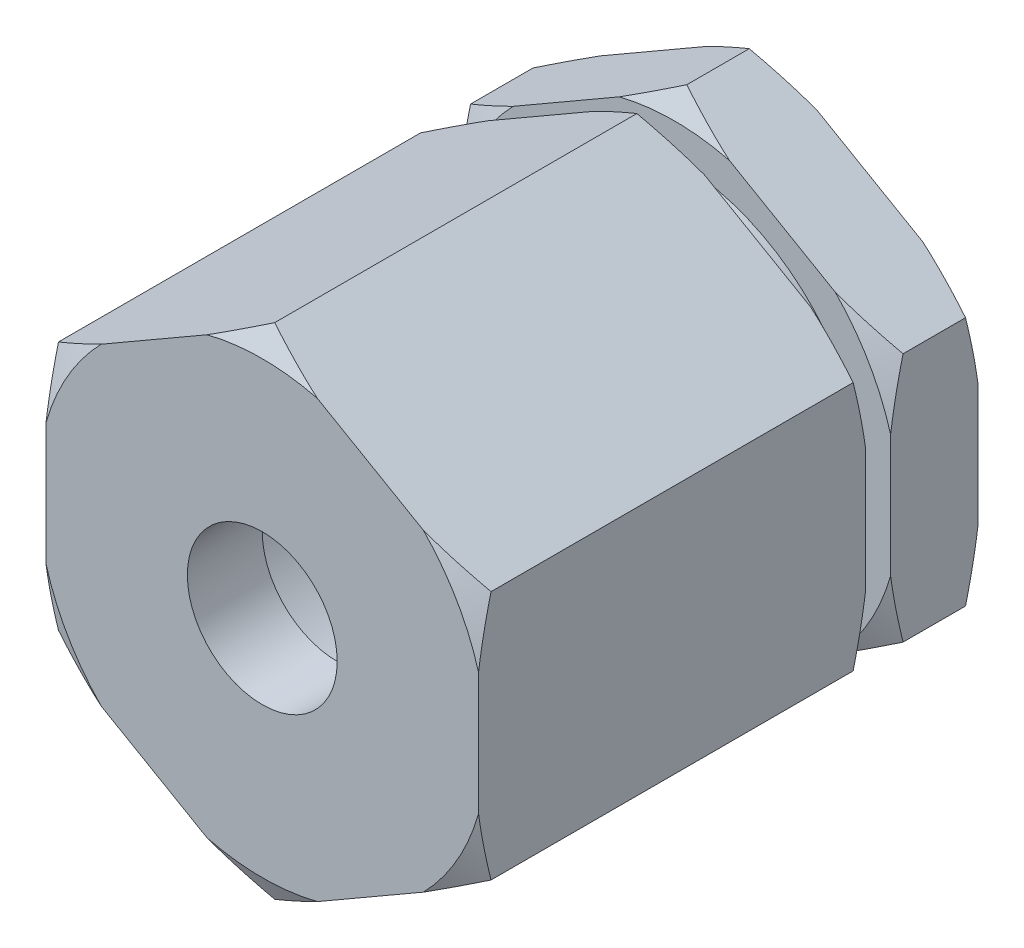
SolidWorks part; units mm, degrees
ref_plane "Plano frontal" through (0, 0, 0) normal (0, 0, 1) x (1, 0, 0)
ref_plane "Plano superior" through (0, 0, 0) normal (0, 1, 0) x (1, 0, 0)
ref_plane "Plano direito" through (0, 0, 0) normal (1, 0, 0) x (0, 0, -1)
sketch "Esboço2" plane through (0, 0, 0) normal (0, 0, 1) x (1, 0, 0)
  line L0 (-8.6603, 5) -> (-8.6603, -5)
  line L5 (8.6603, -5) -> (8.6603, 5)
  line L6 (8.6603, 5) -> (0, 10)
  line L7 (0, 10) -> (-8.6603, 5)
  line L8 (-8.6603, -5) -> (0, -10)
  line L9 (0, -10) -> (8.6603, -5)
  circle A1 centre (0, 0) radius 3
extrude "Ressalto-extrusão1" add sketch "Esboço2" along normal blind 20
sketch "Esboço3" plane through (0, 0, 0) normal (0, 0, -1) x (-1, 0, 0)
  circle A0 centre (0, 0) radius 6
extrude "Corte-extrusão1" cut sketch "Esboço3" against normal blind 17
ref_axis "Eixo1" through (0, 0, 21) along (0, 0, -1)
sketch "Esboço6" plane through (0, 0, 0) normal (0, 1, 0) x (1, 0, 0)
  line L0 (-8.6603, -3.5) -> (-10.0945, -3.5)
  line L1 (-8.6603, -20) -> (-8.6603, 0) construction
  line L2 (-10.0945, -3.5) -> (-10.0945, -4.5)
  line L3 (-8.6603, -4.5) -> (-10.0945, -4.5)
  line L9 (-8.6603, -3.5) -> (-7.6603, -3.5)
  line L10 (-7.6603, -3.5) -> (-7.6603, -4.5)
  line L11 (-7.6603, -4.5) -> (-8.6603, -4.5)
revolve "Corte-Revolução3" cut sketch "Esboço6" angle 360 about axis through (0, 0, 21) along (0, 0, -1)
sketch "Esboço11" plane through (0, 0, 0) normal (1, 0, 0) x (0, 0, -1)
  line L1 (0, 10) -> (0, 5) construction
  line L3 (-3.5, 10) -> (0, 10) construction
  line L4 (0, 9) -> (-0.5, 10)
  line L5 (-3.5, 9) -> (-4.5, 9)
  line L6 (-3, 10) -> (-0.5, 10)
  line L7 (-20, 10) -> (-4.5, 10) construction
  line L8 (-5, 10) -> (-19.5, 10)
  line L9 (-3, 10) -> (-3.5, 9)
  line L10 (-3.5, 10) -> (-3.5, 5) construction
  line L11 (-5, 10) -> (-4.5, 9)
  line L12 (-4.5, 5) -> (-4.5, 10) construction
  line L13 (-19.5, 10) -> (-20, 9)
  line L14 (-20, 10) -> (-20, 5) construction
  line L15 (-20, 9) -> (-20, 10.4562)
  line L16 (-20, 10.4562) -> (0, 10.4562)
  line L17 (0, 10.4562) -> (0, 9)
revolve "Corte-Revolução7" cut sketch "Esboço11" angle 360 about axis through (0, 0, 21) along (0, 0, -1)
